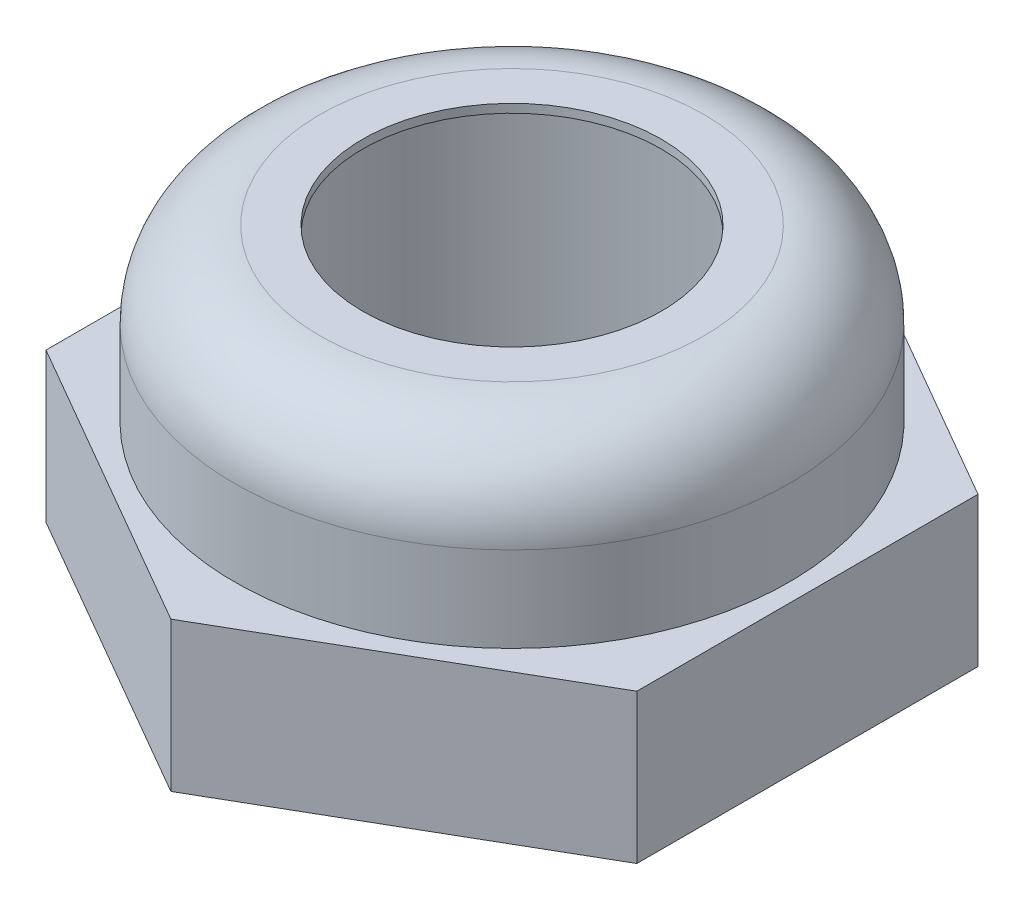
SolidWorks part; units mm, degrees
ref_plane "Спереди (Плоскость XY)" through (0, 0, 0) normal (0, 0, 1) x (1, 0, 0)
ref_plane "Сверху (Плоскость XZ)" through (0, 0, 0) normal (0, 1, 0) x (1, 0, 0)
ref_plane "Справа (Плоскость ZY)" through (0, 0, 0) normal (1, 0, 0) x (0, 0, -1)
sketch "Эскиз1" plane through (0, 0, 0) normal (0, 0, 1) x (1, 0, 0)
  line L0 (0, -7.792) -> (0, 7.4038) construction
  line L1 (-8, -6.9732) -> (-6, -6.9732)
  line L4 (-8, -6.9732) -> (-8, -3.4732)
  line L5 (-3.5, 0.5268) -> (-3.5, 0.3268)
  line L6 (-6.5, -3.4732) -> (-6.5, -1.4732)
  line L7 (-4.5, 0.5268) -> (-3.5, 0.5268)
  line L8 (-6.5, -3.4732) -> (-8, -3.4732)
  line L9 (-6, -6.9732) -> (-6, -0.9732)
  arc A0 (-6.5, -1.4732) -> (-4.5, 0.5268) centre (-4.5, -1.4732) cw
  spline S0 degree 2 poles (-6, -0.9732) (-5.2704, 0.3806) (-3.5, 0.3268) knots 0 0 0 1 1 1
  dimension "D6" = 2
  dimension "D1" = 0.2
  dimension "D2" = 6.5
  dimension "D3" = 6
  dimension "D4" = 3.5
  dimension "D5" = 2
  dimension "D8" = 6
revolve "Повернуть1" add sketch "Эскиз1" angle 360 about L0
sketch "Эскиз2" plane through (0, -3.4732, 0) normal (0, 1, 0) x (1, 0, 0)
  line L0 (0, 8) -> (6.9282, 4)
  line L1 (6.9282, 4) -> (6.9282, -4)
  line L2 (6.9282, -4) -> (0, -8)
  line L3 (0, -8) -> (-6.9282, -4)
  line L4 (-6.9282, -4) -> (-6.9282, 4)
  line L5 (-6.9282, 4) -> (0, 8)
  circle A0 centre (0, 0) radius 8 construction
  circle A1 centre (0, 0) radius 11.6011
  point P0 (0, 8)
  point P1 (6.9282, 4)
  point P6 (6.9282, -4)
  point P7 (0, -8)
  point P8 (-6.9282, -4)
  point P9 (-6.9282, 4)
  point P10 (0, 0)
  dimension "D1" = 6
extrude "Вырез-Вытянуть1" cut sketch "Эскиз2" against normal blind 10
